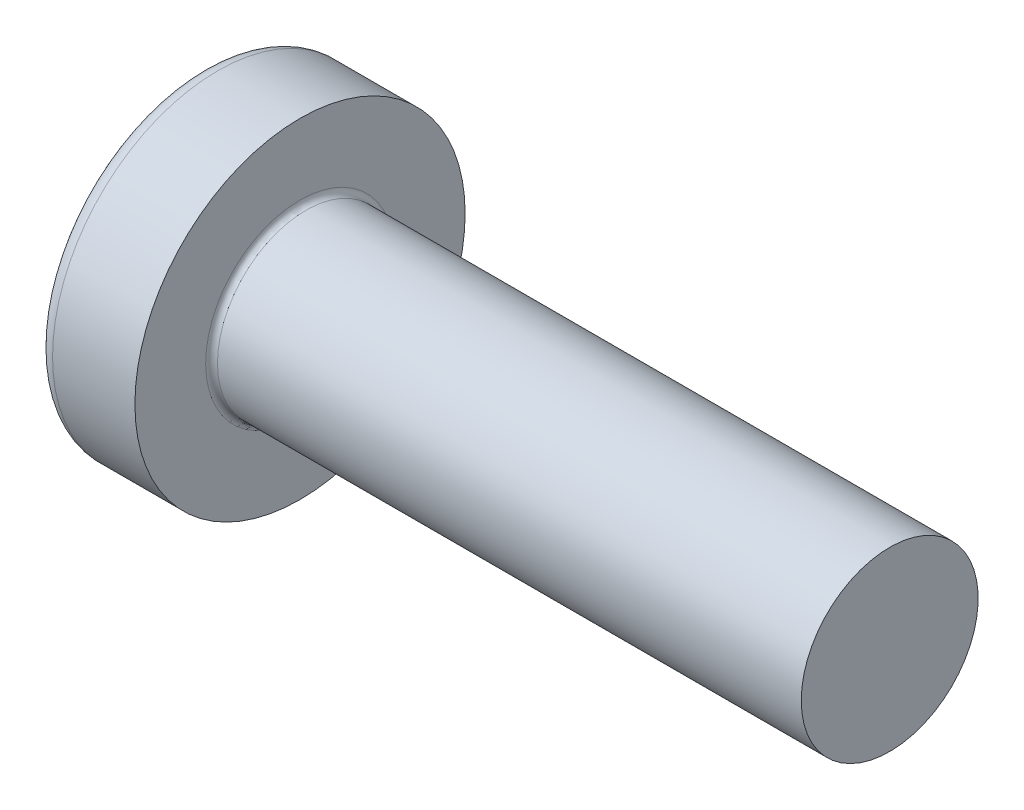
SolidWorks part; units mm, degrees
material "Alliage 7079"
ref_plane "Plane1" through (0, 0, 0) normal (0, 0, 1) x (1, 0, 0)
ref_plane "Plane2" through (0, 0, 0) normal (0, 1, 0) x (1, 0, 0)
ref_plane "Plane3" through (0, 0, 0) normal (1, 0, 0) x (0, 0, -1)
sketch "BodySke" plane through (0, 0, 0) normal (0, 0, 1) x (1, 0, 0)
  line L0 (2.4, 1.5) -> (2.4, 2.8)
  line L1 (2.65, 6.35) -> (2.65, -3.175) construction
  line L2 (-25.4, 0) -> (127, 0) construction
  line L3 (12.4, 0) -> (0, 0)
  line L4 (2.4, 1.5) -> (12.4, 1.5)
  line L5 (12.4, 1.5) -> (12.4, 0)
  line L6 (1.0035, 2.8) -> (2.4, 2.8)
  line L8 (2.4, 6.35) -> (2.4, -3.175) construction
  arc A0 (0.7754, 2.6744) -> (0, 0) centre (5, 0) ccw
  arc A2 (0.7754, 2.6744) -> (1.0035, 2.8) centre (1.0035, 2.53) cw
  dimension "Head_fillet_rad" = 0.27
  dimension "Head_crown_rad" = 5
  dimension "Head_ht" = 2.4
  dimension "Diameter" = 3
  dimension "Length" = 10
  dimension "Head_dia" = 5.6
  dimension "Advance" = 0.5
  dimension "Thread_nom" = 10
revolve "Base-Revolve" add sketch "BodySke"
cosmetic thread "ThreadCosmetic" [suppressed]
fillet "Fillet1" radius 0.1 1 edges at (2.4, 0, 1.5)
sketch "Sketch3" plane through (0, 0, 0) normal (1, 0, 0) x (0, 0, -1)
  line L0 (0.37, -1.4) -> (-0.37, -1.4)
  line L1 (0.37, -1.4) -> (0.37, 1.4)
  line L2 (-0.37, 1.4) -> (0.37, 1.4)
  line L3 (-0.37, 1.4) -> (-0.37, -1.4)
  dimension "D1" = 1.4
  dimension "Cross_dia" = 2.8
  dimension "D2" = 0.37
  dimension "Cross_width" = 0.74
ref_plane "Plane4" through (1.75, 0, 0) normal (1, 0, 0) x (0, 0, -1)
sketch "Sketch4" plane through (1.75, 0, 0) normal (1, 0, 0) x (0, 0, -1)
  line L0 (0.37, -0.5275) -> (-0.37, -0.5275)
  line L1 (0.37, -0.5275) -> (0.37, 0.5275)
  line L2 (-0.37, 0.5275) -> (0.37, 0.5275)
  line L3 (-0.37, 0.5275) -> (-0.37, -0.5275)
  dimension "D1" = 0.74
  dimension "D2" = 1.055
  dimension "D3" = 0.37
  dimension "D4" = 0.5275
loft "Recess" cut profiles "Sketch3", "Sketch4"
pattern_circular "RecPat" count 2 every 90 about axis through (0, 0, 0) along (1, 0, 0) of "Recess"
sketch "RecCorSke" plane through (0, 0, 0) normal (0, 0, 1) x (1, 0, 0)
  line L0 (-3.175, 0) -> (15.875, 0) construction
  line L1 (-25.4, 0) -> (127, 0) construction
  line L2 (0, 0) -> (0, 0.6784)
  line L3 (0, 0.6784) -> (1.75, 0.556)
  line L4 (1.75, 0.556) -> (1.9307, 0)
  line L5 (1.9307, 0) -> (0, 0)
  dimension "Diameter" = 1.112
  dimension "Depth" = 1.75
  dimension "Draft_angle" = 4
  dimension "Bottom_angle" = 18
revolve "RecessCore" cut sketch "RecCorSke" angle 360 about L0
sketch "ThdSchSke" plane through (0, 0, 0) normal (0, 0, 1) x (1, 0, 0)
  line L0 (3.4, -1.2195) -> (3.2036, -1.5)
  line L1 (3.4, -1.2195) -> (3.5964, -1.5)
  line L2 (3.5964, -1.5) -> (3.5964, -1.875)
  line L3 (-3.175, 0) -> (5.1513, 0) construction
  line L5 (3.5964, -1.875) -> (3.2036, -1.875)
  line L6 (3.2036, -1.875) -> (3.2036, -1.5)
  dimension "Thread_minor" = 2.439
  dimension "Diameter" = 3
  dimension "Start" = 3.4
  dimension "SideAngle" = 55
  dimension "VeeAngle" = 70
  dimension "Overcut" = 3.75
revolve "ThreadSchematic" [suppressed] cut sketch "ThdSchSke" angle 360 about L3
pattern_linear "ThdSchPat" [suppressed]
equation "\"D1@Sketch3\" = \"Cross_dia@Sketch3\" / 2"
equation "\"D2@Sketch3\" = \"Cross_width@Sketch3\" / 2"
equation "\"Depth@RecCorSke\" = \"Cross_depth@Plane4\""
equation "\"D1@Sketch4\" = \"Cross_width@Sketch3\""
equation "\"D2@Sketch4\" = \"Cross_dia@Sketch3\" - 2.0 * \"Cross_depth@Plane4\" * tan(26.5  * 0.017453292)"
equation "\"D3@Sketch4\" = \"D1@Sketch4\" / 2"
equation "\"D4@Sketch4\" = \"D2@Sketch4\" / 2"
equation "\"Thread_length@ThreadCosmetic\" = ((sgn( (\"Length@BodySke\" - \"Advance@BodySke\" * 2.0 ) - \"Thread_nom@BodySke\" )-1)*( (\"Length@BodySke\" - \"Advance@BodySke\" * 2.0 ) - \"Thread_nom@BodySke\" ))/-2+ \"Thread_nom@BodySke\""
equation "\"Thread_minor@ThdSchSke\" = \"Thread_minor@ThreadCosmetic\""
equation "\"Diameter@ThdSchSke\" = \"Diameter@BodySke\""
equation "\"Overcut@ThdSchSke\" = \"Diameter@BodySke\" * 1.25"
equation "\"Start@ThdSchSke\" = \"Head_ht@BodySke\" + \"Length@BodySke\" - \"Thread_length@ThreadCosmetic\"  '---Non-countersunk---"
equation "\"Num_threads@ThdSchPat\" = int( \"Thread_length@ThreadCosmetic\" / \"Advance@BodySke\" + 0.999 )  + 1"
equation "\"Advance@ThdSchPat\" = \"Thread_length@ThreadCosmetic\" /  (\"Num_threads@ThdSchPat\" - 1) 'relax it"
